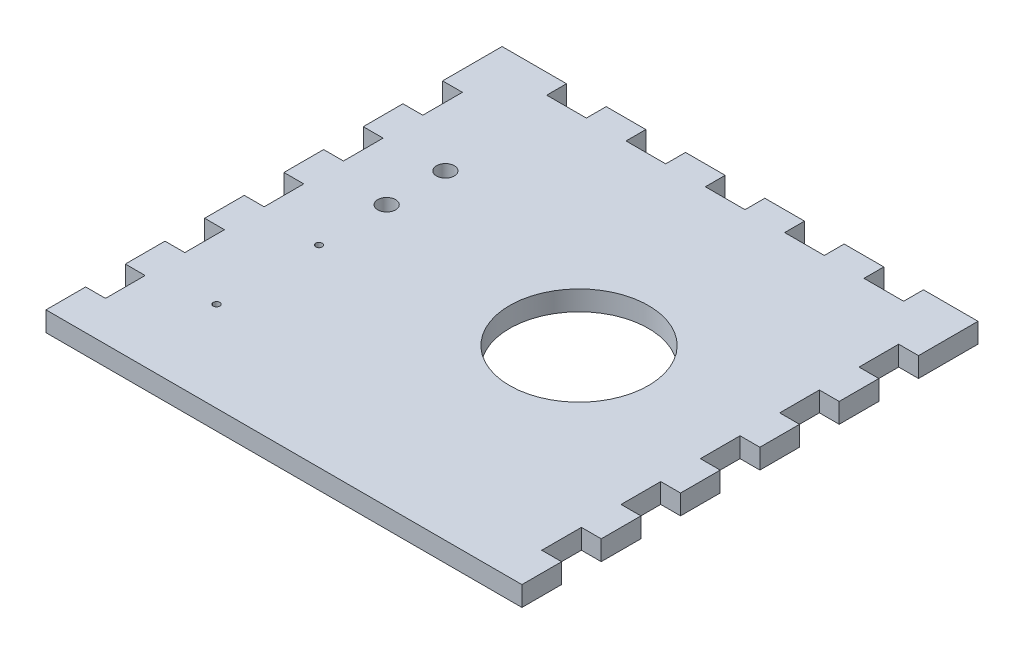
SolidWorks part; units mm, degrees
ref_plane "Front Plane" through (0, 0, 0) normal (0, 0, 1) x (1, 0, 0)
ref_plane "Top Plane" through (0, 0, 0) normal (0, 1, 0) x (1, 0, 0)
ref_plane "Right Plane" through (0, 0, 0) normal (1, 0, 0) x (0, 0, -1)
sketch "Sketch1" plane through (0, 0, 0) normal (0, 1, 0) x (1, 0, 0)
  line L1 (-139.7, -139.7) -> (139.7, -139.7)
  line L2 (-139.7, -139.7) -> (-139.7, 139.7)
  line L3 (-139.7, 139.7) -> (139.7, 139.7)
  line L4 (139.7, -139.7) -> (139.7, 139.7)
  line L5 (-139.7, -139.7) -> (139.7, 139.7) construction
  line L6 (-139.7, 139.7) -> (139.7, -139.7) construction
  point P0 (0, 0)
  dimension "D1" = 279.4
  dimension "D2" = 279.4
extrude "Boss-Extrude1" add sketch "Sketch1" along normal blind 12.7
sketch "Sketch2" plane through (139.7, 0, 0) normal (1, 0, 0) x (0, 0, -1)
  line L0 (-139.7, 12.7) -> (139.7, 12.7) construction
  line L1 (-139.7, 0) -> (-114.3, 0)
  line L2 (-139.7, 0) -> (-139.7, 12.7)
  line L3 (-139.7, 12.7) -> (-114.3, 12.7)
  line L4 (-114.3, 0) -> (-114.3, 12.7)
  dimension "D1" = 25.4
extrude "Boss-Extrude2" add sketch "Sketch2" along normal blind 12.7
pattern_linear "LPattern1" count 6 spacing 50.8 along (0, 0, -1) of "Boss-Extrude2"
mirror "Mirror1" about plane through (0, 0, 0) normal (1, 0, 0) of "LPattern1", "Boss-Extrude2"
sketch "Sketch3" plane through (0, 0, -139.7) normal (0, 0, -1) x (-1, 0, 0)
  line L0 (-152.4, 12.7) -> (152.4, 12.7) construction
  line L1 (-142.875, 12.7) -> (-117.475, 12.7)
  line L2 (-142.875, 12.7) -> (-142.875, 0)
  line L3 (-142.875, 0) -> (-117.475, 0)
  line L4 (-117.475, 12.7) -> (-117.475, 0)
  line L5 (-152.4, 0) -> (152.4, 0) construction
  line L6 (-152.4, 0) -> (-152.4, 12.7) construction
  dimension "D1" = 9.525
  dimension "D2" = 25.4
extrude "Boss-Extrude3" add sketch "Sketch3" along normal blind 12.7
pattern_linear "LPattern2" count 6 spacing 50.8 along (-1, 0, 0) of "Boss-Extrude3"
sketch "Sketch5" plane through (0, 0, -139.7) normal (0, 0, -1) x (-1, 0, 0)
  line L6 (160.655, 0) -> (-160.655, 0) construction
  line L7 (-152.4, 12.7) -> (-135.3964, 12.7)
  line L8 (-152.4, 12.7) -> (-152.4, 0)
  line L9 (-152.4, 0) -> (-135.3964, 0)
  line L10 (-135.3964, 12.7) -> (-135.3964, 0)
extrude "Boss-Extrude4" add sketch "Sketch5" along normal blind 12.7
mirror "Mirror2" about plane through (0, 0, 0) normal (1, 0, 0) of "Boss-Extrude4"
sketch "Sketch6" plane through (0, 12.7, 0) normal (0, 1, 0) x (1, 0, 0)
  line L0 (66.675, 139.7) -> (41.275, 139.7) construction
  line L1 (139.7, -12.7) -> (139.7, 12.7) construction
  circle A0 centre (38.1, 11.176) radius 44.45
  dimension "D1" = 128.524
  dimension "D2" = 101.6
extrude "Cut-Extrude1" cut sketch "Sketch6" against normal through all
sketch "Sketch7" plane through (0, 12.7, 0) normal (0, 1, 0) x (1, 0, 0)
  line L0 (-139.7, 63.5) -> (-139.7, 38.1) construction
  line L1 (-139.7, 114.3) -> (-139.7, 88.9) construction
  line L2 (-85.725, 139.7) -> (-111.125, 139.7) construction
  circle A0 centre (-101.6, 65.278) radius 5.715
  circle A1 centre (-101.6, 27.686) radius 5.715
  dimension "D1" = 11.43
  dimension "D2" = 11.43
  dimension "D3" = 38.1
  dimension "D4" = 38.1
  dimension "D5" = 37.592
  dimension "D6" = 74.422
extrude "Cut-Extrude2" cut sketch "Sketch7" against normal through all
sketch "Sketch8" plane through (0, 12.7, 0) normal (0, 1, 0) x (1, 0, 0)
  circle A0 centre (-100.9, -81.9861) radius 2.1 construction
  circle A1 centre (-100.9, -81.9861) radius 2.1
  circle A2 centre (-100.9, -16.3789) radius 2.1 construction
  circle A3 centre (-100.9, -16.3789) radius 2.1
extrude "Cut-Extrude3" cut sketch "Sketch8" against normal through all
sketch "Sketch9" plane through (0, 12.7, 0) normal (0, 1, 0) x (1, 0, 0)
  circle A0 centre (80.3243, 112.3205) radius 12.1113
  circle A1 centre (80.3243, 112.3205) radius 15.9341
  circle A2 centre (118.6769, 96.3864) radius 9.3629
  circle A3 centre (118.6769, 96.3864) radius 13.2353
